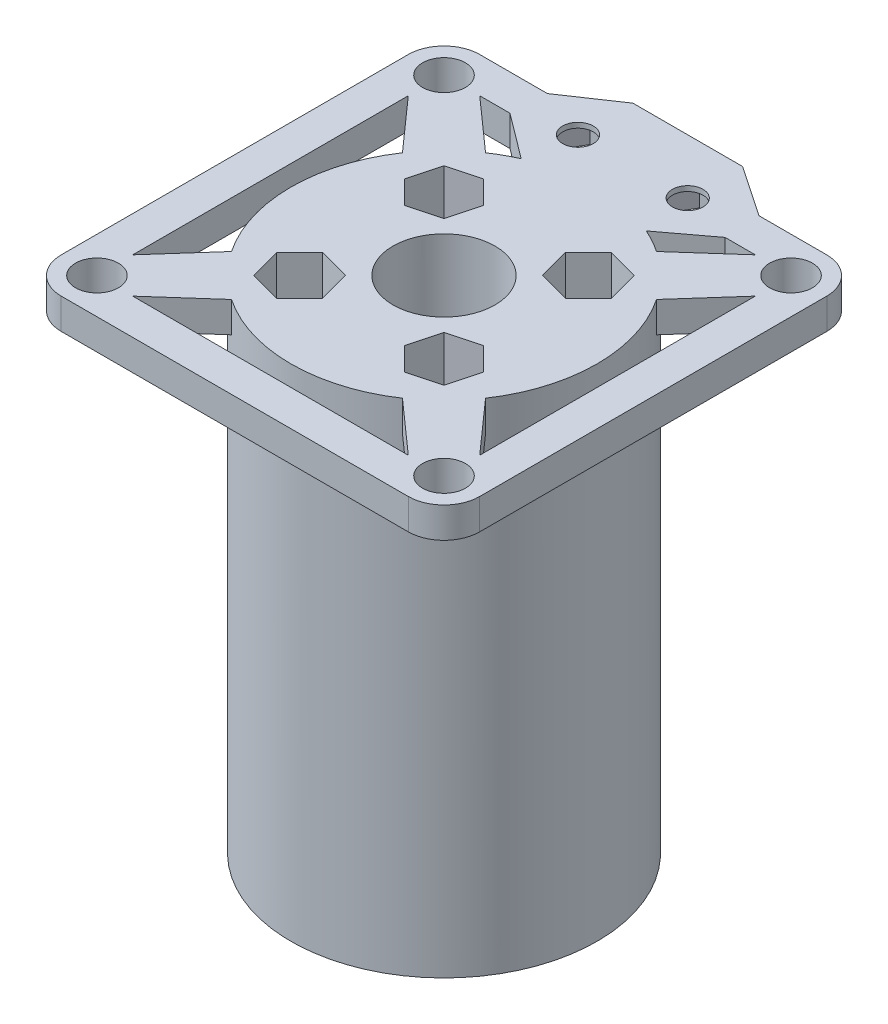
SolidWorks part; units mm, degrees
ref_plane "前视基准面" through (0, 0, 0) normal (0, 0, 1) x (1, 0, 0)
ref_plane "上视基准面" through (0, 0, 0) normal (0, 1, 0) x (1, 0, 0)
ref_plane "右视基准面" through (0, 0, 0) normal (1, 0, 0) x (0, 0, -1)
sketch "草图1" plane through (0, 0, 0) normal (0, 1, 0) x (1, 0, 0)
  circle A0 centre (-5.3729, -8.9317) radius 15
  circle A1 centre (-22.3729, 8.0683) radius 2.1
  circle A5 centre (-5.3729, -8.9317) radius 5
  circle A6 centre (-22.3729, 8.0683) radius 3.5
  dimension "D4" = 4.2
  dimension "D8" = 10
  dimension "D9" = 7
extrude "凸台-拉伸4" add sketch "草图1" along normal blind 3
sketch "草图5" plane through (0, 0, 0) normal (0, 1, 0) x (1, 0, 0)
  line L0 (-22.3729, 4.5683) -> (-10.3729, -8.9317)
  line L1 (-5.3729, -3.9317) -> (-18.8729, 8.0683)
  line L2 (-18.8729, 8.0683) -> (-22.3729, 4.5683)
  line L3 (-10.3729, -8.9317) -> (-10.3729, -3.9317)
  line L4 (-10.3729, -3.9317) -> (-5.3729, -3.9317)
  circle A0 centre (-22.3729, 8.0683) radius 3.5 construction
  circle A1 centre (-5.3729, -8.9317) radius 5 construction
extrude "凸台-拉伸5" add sketch "草图5" along normal blind 3
pattern_circular "阵列(圆周)2" count 4 over 360 about axis through (-5.3729, 0, 8.9317) along (0, 1, 0) of "凸台-拉伸5"
sketch "草图6" plane through (0, 3, 0) normal (0, 1, 0) x (1, 0, 0)
  circle A0 centre (11.6271, 8.0683) radius 2.1
  circle A1 centre (11.6271, 8.0683) radius 3.5
  dimension "D2" = 4.2
  dimension "D3" = 7
extrude "凸台-拉伸6" add sketch "草图6" against normal blind 3
pattern_circular "阵列(圆周)3" count 4 over 360 about axis through (-5.3729, 0, 8.9317) along (0, 1, 0) of "凸台-拉伸6"
sketch "草图7" plane through (0, 0, 0) normal (0, -1, 0) x (1, 0, 0)
  circle A0 centre (-5.3729, 8.9317) radius 15
  circle A1 centre (-5.3729, 8.9317) radius 5
extrude "凸台-拉伸7" add sketch "草图7" along normal blind 46
sketch "草图8" plane through (0, -46, 0) normal (0, -1, 0) x (1, 0, 0)
  line L4 (3.9435, 18.2482) -> (0.8763, 19.07)
  line L5 (0.8763, 19.07) -> (-1.3691, 16.8247)
  line L6 (-1.3691, 16.8247) -> (-0.5472, 13.7574)
  line L7 (-0.5472, 13.7574) -> (2.52, 12.9356)
  line L8 (2.52, 12.9356) -> (4.7654, 15.1809)
  line L9 (4.7654, 15.1809) -> (3.9435, 18.2482)
  circle A3 centre (1.6982, 16.0028) radius 2.75 construction
  dimension "D1" = 5.5
sketch "草图9" plane through (0, 3, 0) normal (0, 1, 0) x (1, 0, 0)
  line L0 (0.8763, -19.07) -> (-1.3691, -16.8247) construction
  line L1 (3.9435, -18.2482) -> (0.8763, -19.07) construction
  line L2 (4.7654, -15.1809) -> (3.9435, -18.2482) construction
  line L3 (2.52, -12.9356) -> (4.7654, -15.1809) construction
  line L4 (-0.5472, -13.7574) -> (2.52, -12.9356) construction
  line L5 (-1.3691, -16.8247) -> (-0.5472, -13.7574) construction
  line L6 (0.8763, -19.07) -> (-1.3691, -16.8247)
  line L7 (3.9435, -18.2482) -> (0.8763, -19.07)
  line L8 (4.7654, -15.1809) -> (3.9435, -18.2482)
  line L9 (2.52, -12.9356) -> (4.7654, -15.1809)
  line L10 (-0.5472, -13.7574) -> (2.52, -12.9356)
  line L11 (-1.3691, -16.8247) -> (-0.5472, -13.7574)
extrude "切除-拉伸1" cut sketch "草图9" against normal blind 46
pattern_circular "阵列(圆周)4" count 4 over 360 about axis through (-5.3729, 0, 8.9317) along (0, 1, 0) of "切除-拉伸1"
sketch "草图11" plane through (0, -43, 0) normal (0, 1, 0) x (1, 0, 0)
  circle A0 centre (1.6982, -1.8607) radius 1.5
  dimension "D1" = 3
extrude "切除-拉伸2" cut sketch "草图11" against normal blind 3
pattern_circular "阵列(圆周)5" count 4 over 360 about axis through (-5.3729, 0, 8.9317) along (0, 1, 0) of "切除-拉伸2"
sketch "草图12" plane through (0, 3, 0) normal (0, 1, 0) x (1, 0, 0)
  line L0 (15.1271, 8.0683) -> (15.1271, -25.9317)
  line L1 (15.1271, -25.9317) -> (11.6271, -22.4317)
  line L2 (11.6271, -22.4317) -> (11.6271, 4.5683)
  line L3 (11.6271, 4.5683) -> (15.1271, 8.0683)
  arc A0 (11.6271, 4.5683) -> (8.1271, 8.0683) centre (11.6271, 8.0683) ccw construction
  arc A1 (8.1271, -25.9317) -> (11.6271, -22.4317) centre (11.6271, -25.9317) ccw construction
extrude "凸台-拉伸8" add sketch "草图12" against normal blind 3
sketch "草图13" plane through (0, 3, 0) normal (0, 1, 0) x (1, 0, 0)
  line L0 (11.6271, 11.5683) -> (-22.3729, 11.5683)
  line L1 (-22.3729, 11.5683) -> (-18.8729, 8.0683)
  line L2 (-18.8729, 8.0683) -> (8.1271, 8.0683)
  line L3 (8.1271, 8.0683) -> (11.6271, 11.5683)
  arc A0 (15.1271, 8.0683) -> (8.1271, 8.0683) centre (11.6271, 8.0683) ccw construction
  arc A1 (-18.8729, 8.0683) -> (-22.3729, 4.5683) centre (-22.3729, 8.0683) ccw construction
extrude "凸台-拉伸9" add sketch "草图13" against normal blind 3
sketch "草图14" plane through (0, 3, 0) normal (0, 1, 0) x (1, 0, 0)
  line L0 (-25.8729, 8.0683) -> (-25.8729, -25.9317)
  line L1 (-25.8729, -25.9317) -> (-22.3729, -22.4317)
  line L2 (-22.3729, -22.4317) -> (-22.3729, 4.5683)
  line L3 (-22.3729, 4.5683) -> (-25.8729, 8.0683)
  arc A0 (-22.3729, 11.5683) -> (-22.3729, 4.5683) centre (-22.3729, 8.0683) ccw construction
  arc A1 (-22.3729, -22.4317) -> (-18.8729, -25.9317) centre (-22.3729, -25.9317) ccw construction
extrude "凸台-拉伸10" add sketch "草图14" against normal blind 3
sketch "草图15" plane through (0, 3, 0) normal (0, 1, 0) x (1, 0, 0)
  line L0 (-22.3729, -29.4317) -> (11.6271, -29.4317)
  line L1 (11.6271, -29.4317) -> (8.1271, -25.9317)
  line L2 (8.1271, -25.9317) -> (-18.8729, -25.9317)
  line L3 (-18.8729, -25.9317) -> (-22.3729, -29.4317)
  arc A0 (-25.8729, -25.9317) -> (-18.8729, -25.9317) centre (-22.3729, -25.9317) ccw construction
  arc A1 (8.1271, -25.9317) -> (15.1271, -25.9317) centre (11.6271, -25.9317) ccw construction
extrude "凸台-拉伸11" add sketch "草图15" against normal blind 3
sketch "草图16" plane through (0, 0, 0) normal (0, -1, 0) x (1, 0, 0)
  line L0 (-10.7479, -4.1933) -> (0.0021, -4.1933)
  line L1 (0.0021, -4.1933) -> (5.1636, -8.0683)
  line L2 (-18.8729, -8.0683) -> (8.1271, -8.0683) construction
  line L3 (4.9912, -11.5683) -> (0.0021, -14.9433)
  line L4 (11.6271, -11.5683) -> (-22.3729, -11.5683) construction
  line L5 (-7.5725, -9.5683) -> (-9.1602, -6.8183)
  line L6 (-9.1602, -6.8183) -> (-12.3356, -6.8183)
  line L7 (-12.3356, -6.8183) -> (-13.9233, -9.5683)
  line L8 (-13.9233, -9.5683) -> (-12.3356, -12.3183)
  line L9 (-12.3356, -12.3183) -> (-9.1602, -12.3183)
  line L10 (-9.1602, -12.3183) -> (-7.5725, -9.5683)
  line L11 (3.1775, -9.5683) -> (1.5898, -6.8183)
  line L12 (1.5898, -6.8183) -> (-1.5856, -6.8183)
  line L13 (-1.5856, -6.8183) -> (-3.1733, -9.5683)
  line L14 (-3.1733, -9.5683) -> (-1.5856, -12.3183)
  line L15 (-1.5856, -12.3183) -> (1.5898, -12.3183)
  line L16 (1.5898, -12.3183) -> (3.1775, -9.5683)
  line L17 (0.0021, -14.9433) -> (-10.7479, -14.9433)
  line L18 (-10.7479, -14.9433) -> (-15.7369, -11.5683)
  line L19 (-15.7369, -11.5683) -> (-15.9094, -8.0683)
  line L20 (-15.9094, -8.0683) -> (-10.7479, -4.1933)
  line L21 (4.9912, -11.5683) -> (5.1636, -8.0683)
  circle A0 centre (-10.7479, -9.5683) radius 2.75 construction
  circle A2 centre (0.0021, -9.5683) radius 2.75 construction
  dimension "D4" = 5.5
  dimension "D5" = 5.5
sketch "草图17" plane through (0, 0, 0) normal (0, -1, 0) x (1, 0, 0)
  line L1 (-7.5725, -9.5683) -> (-9.1602, -6.8183)
  line L2 (-9.1602, -6.8183) -> (-12.3356, -6.8183)
  line L3 (-12.3356, -6.8183) -> (-13.9233, -9.5683)
  line L4 (-13.9233, -9.5683) -> (-12.3356, -12.3183)
  line L5 (-12.3356, -12.3183) -> (-9.1602, -12.3183)
  line L6 (-9.1602, -12.3183) -> (-7.5725, -9.5683)
  line L7 (3.1775, -9.5683) -> (1.5898, -6.8183)
  line L8 (1.5898, -6.8183) -> (-1.5856, -6.8183)
  line L9 (-1.5856, -6.8183) -> (-3.1733, -9.5683)
  line L10 (-3.1733, -9.5683) -> (-1.5856, -12.3183)
  line L11 (-1.5856, -12.3183) -> (1.5898, -12.3183)
  line L12 (1.5898, -12.3183) -> (3.1775, -9.5683)
  circle A0 centre (-10.7479, -9.5683) radius 2.75 construction
  circle A1 centre (0.0021, -9.5683) radius 2.75 construction
extrude "凸台-拉伸13" add sketch "草图16" against normal blind 3
sketch "草图18" plane through (0, 0, 0) normal (0, -1, 0) x (1, 0, 0)
  line L1 (-7.5725, -9.5683) -> (-9.1602, -6.8183)
  line L2 (-9.1602, -6.8183) -> (-12.3356, -6.8183)
  line L3 (-12.3356, -6.8183) -> (-13.9233, -9.5683)
  line L4 (-13.9233, -9.5683) -> (-12.3356, -12.3183)
  line L5 (-12.3356, -12.3183) -> (-9.1602, -12.3183)
  line L6 (-9.1602, -12.3183) -> (-7.5725, -9.5683)
  line L7 (3.1775, -9.5683) -> (1.5898, -6.8183)
  line L8 (1.5898, -6.8183) -> (-1.5856, -6.8183)
  line L9 (-1.5856, -6.8183) -> (-3.1733, -9.5683)
  line L10 (-3.1733, -9.5683) -> (-1.5856, -12.3183)
  line L11 (-1.5856, -12.3183) -> (1.5898, -12.3183)
  line L12 (1.5898, -12.3183) -> (3.1775, -9.5683)
  circle A0 centre (-10.7479, -9.5683) radius 2.75 construction
  circle A1 centre (0.0021, -9.5683) radius 2.75 construction
extrude "凸台-拉伸14" add sketch "草图18" against normal blind 3
extrude "切除-拉伸3" cut sketch "草图17" against normal blind 2.5
sketch "草图19" plane through (0, 2.5, 0) normal (0, -1, 0) x (1, 0, 0)
  circle A0 centre (0.0021, -9.5683) radius 1.5
  dimension "D1" = 3
extrude "切除-拉伸4" cut sketch "草图19" against normal blind 2.5
sketch "草图20" plane through (0, 2.5, 0) normal (0, -1, 0) x (1, 0, 0)
  circle A0 centre (-10.7479, -9.5683) radius 1.5
  dimension "D1" = 3
extrude "切除-拉伸5" cut sketch "草图20" against normal blind 2.5
sketch "草图21" plane through (0, 0, 0) normal (0, 1, 0) x (1, 0, 0)
  circle A0 centre (59.6655, -8.9317) radius 15
  circle A1 centre (59.6655, -8.9317) radius 5
  dimension "D1" = 30
  dimension "D2" = 10
extrude "凸台-拉伸15" add sketch "草图21" along normal blind 3 separate body
sketch "草图22" plane through (0, 0, 0) normal (0, -1, 0) x (1, 0, 0)
  circle A0 centre (59.6655, 18.9317) radius 1.5
  dimension "D2" = 3
extrude "切除-拉伸6" cut sketch "草图22" against normal blind 3
pattern_circular "阵列(圆周)6" count 4 over 360 about axis through (59.6655, 0, 8.9317) along (0, 1, 0) of "切除-拉伸6"
extrude "凸台-拉伸16" add sketch "草图8" along normal blind 3
sketch "草图24" plane through (0, -49, 0) normal (0, -1, 0) x (1, 0, 0)
  line L1 (4.7654, 15.1809) -> (3.9435, 18.2482)
  line L2 (3.9435, 18.2482) -> (0.8763, 19.07)
  line L3 (0.8763, 19.07) -> (-1.3691, 16.8247)
  line L4 (-1.3691, 16.8247) -> (-0.5472, 13.7574)
  line L5 (-0.5472, 13.7574) -> (2.52, 12.9356)
  line L6 (2.52, 12.9356) -> (4.7654, 15.1809)
  circle A0 centre (1.6982, 16.0028) radius 2.75 construction
extrude "切除-拉伸7" cut sketch "草图24" against normal blind 3
sketch "草图25" plane through (0, 0, 0) normal (0, -1, 0) x (1, 0, 0)
  circle A0 centre (59.6655, 8.9317) radius 15
  circle A1 centre (59.6655, 8.9317) radius 5
extrude "凸台-拉伸17" add sketch "草图25" along normal blind 43
sketch "草图27" plane through (0, 3, 0) normal (0, 1, 0) x (1, 0, 0)
  circle A0 centre (59.6655, 1.0683) radius 1.5
  circle A1 centre (69.6655, -8.9317) radius 1.5
  circle A2 centre (59.6655, -18.9317) radius 1.5
  circle A3 centre (49.6655, -8.9317) radius 1.5
extrude "切除-拉伸8" cut sketch "草图27" against normal blind 46
sketch "草图28" plane through (0, -43, 0) normal (0, -1, 0) x (1, 0, 0)
  circle A0 centre (59.6655, 18.9317) radius 2.75
  circle A1 centre (49.6655, 8.9317) radius 2.75
  circle A2 centre (59.6655, -1.0683) radius 2.75
  circle A3 centre (69.6655, 8.9317) radius 2.75
  dimension "D1" = 5.5
  dimension "D2" = 5.5
  dimension "D3" = 5.5
  dimension "D4" = 5.5
extrude "切除-拉伸9" cut sketch "草图28" against normal blind 43
sketch "草图29" plane through (0, 3, 0) normal (0, 1, 0) x (1, 0, 0)
  circle A0 centre (66.7366, -1.8607) radius 1.5
  dimension "D2" = 3
extrude "切除-拉伸10" cut sketch "草图29" against normal blind 46
pattern_circular "阵列(圆周)7" count 4 over 360 about axis through (59.6655, 0, 8.9317) along (0, 1, 0) of "切除-拉伸10"
sketch "草图30" plane through (0, 3, 0) normal (0, 1, 0) x (1, 0, 0)
  line L2 (64.4912, -4.106) -> (67.5585, -4.9279)
  line L3 (67.5585, -4.9279) -> (69.8038, -2.6825)
  line L4 (69.8038, -2.6825) -> (68.982, 0.3847)
  line L5 (68.982, 0.3847) -> (65.9148, 1.2066)
  line L6 (65.9148, 1.2066) -> (63.6694, -1.0388)
  line L7 (63.6694, -1.0388) -> (64.4912, -4.106)
  circle A0 centre (66.7366, -1.8607) radius 2.75 construction
  dimension "D1" = 5.5
extrude "切除-拉伸11" cut sketch "草图30" against normal blind 43
pattern_circular "阵列(圆周)8" count 4 over 360 about axis through (59.6655, 0, 8.9317) along (0, 1, 0) of "切除-拉伸11"
sketch "草图31" plane through (0, 3, 0) normal (0, 1, 0) x (1, 0, 0)
  circle A0 centre (59.6655, -8.9317) radius 26.2442
extrude "切除-拉伸12" cut sketch "草图31" against normal blind 100
